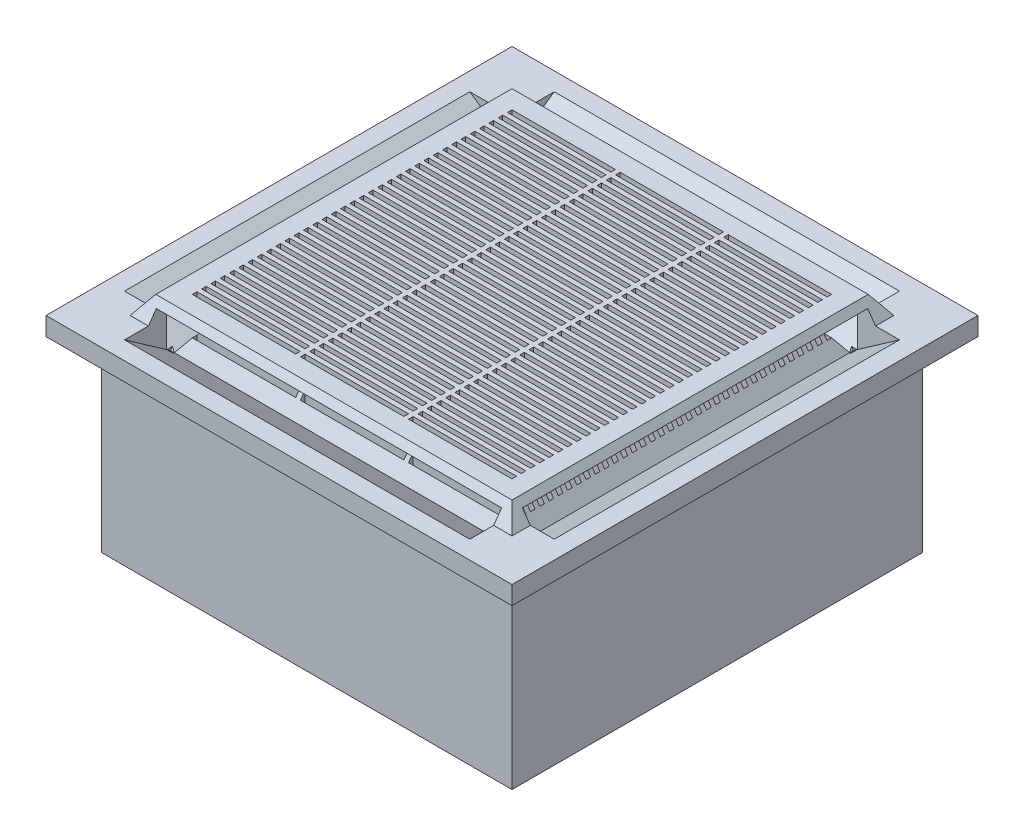
SolidWorks part; units mm, degrees
material "ABS"
ref_plane "Front Plane" through (0, 0, 0) normal (0, 0, 1) x (1, 0, 0)
ref_plane "Top Plane" through (0, 0, 0) normal (0, 1, 0) x (1, 0, 0)
ref_plane "Right Plane" through (0, 0, 0) normal (1, 0, 0) x (0, 0, -1)
sketch "Sketch1" plane through (0, 0, 0) normal (0, 1, 0) x (1, 0, 0)
  line L1 (-284.988, 284.988) -> (284.988, 284.988)
  line L2 (-284.988, 284.988) -> (-284.988, -284.988)
  line L3 (-284.988, -284.988) -> (284.988, -284.988)
  line L4 (284.988, 284.988) -> (284.988, -284.988)
  point P4 (0, 284.988)
  point P7 (-284.988, 0)
  dimension "D1" = 569.976
  dimension "D2" = 569.976
extrude "Boss-Extrude1" add sketch "Sketch1" along normal blind 260.096
sketch3d "3DSketch1"
  point P0 (-88.2401, 260.096, -68.0252)
ref_plane "Plane1" through (0, 260.096, 0) normal (0, 1, 0) x (1, 0, 0)
sketch "Sketch3" plane through (0, 260.096, 0) normal (0, 1, 0) x (1, 0, 0)
  line L1 (-322.961, 322.961) -> (323.977, 322.961)
  line L2 (-322.961, 322.961) -> (-322.961, -323.977)
  line L3 (-322.961, -323.977) -> (323.977, -323.977)
  line L4 (323.977, 322.961) -> (323.977, -323.977)
  dimension "D1" = 646.938
  dimension "D2" = 646.938
  dimension "D3" = 38.989
  dimension "D4" = 38.989
extrude "Boss-Extrude2" add sketch "Sketch3" along normal blind 50.8
sketch "Sketch4" plane through (0, 310.896, 0) normal (0, 1, 0) x (1, 0, 0)
  line L0 (-322.961, 322.961) -> (-322.961, -323.977) construction
  line L1 (-221.361, 221.361) -> (-77.851, 221.361)
  line L2 (-221.361, 221.361) -> (-221.361, 215.011)
  line L3 (-221.361, 215.011) -> (-77.851, 215.011)
  line L4 (-77.851, 221.361) -> (-77.851, 215.011)
  line L5 (323.977, 322.961) -> (-322.961, 322.961) construction
  line L6 (-71.247, 221.361) -> (72.263, 221.361)
  line L7 (-71.247, 221.361) -> (-71.247, 215.011)
  line L8 (-71.247, 215.011) -> (72.263, 215.011)
  line L9 (72.263, 221.361) -> (72.263, 215.011)
  line L10 (78.867, 221.361) -> (222.377, 221.361)
  line L11 (78.867, 221.361) -> (78.867, 215.011)
  line L12 (78.867, 215.011) -> (222.377, 215.011)
  line L13 (222.377, 221.361) -> (222.377, 215.011)
  line L14 (-71.247, 208.4966) -> (72.263, 208.4966)
  line L15 (-71.247, 208.4966) -> (-71.247, 202.1466)
  line L16 (-71.247, 202.1466) -> (72.263, 202.1466)
  line L17 (72.263, 208.4966) -> (72.263, 202.1466)
  line L18 (78.867, 208.4966) -> (222.377, 208.4966)
  line L19 (78.867, 208.4966) -> (78.867, 202.1466)
  line L20 (78.867, 202.1466) -> (222.377, 202.1466)
  line L21 (222.377, 208.4966) -> (222.377, 202.1466)
  line L22 (-71.247, 195.6323) -> (72.263, 195.6323)
  line L23 (-71.247, 195.6323) -> (-71.247, 189.2823)
  line L24 (-71.247, 189.2823) -> (72.263, 189.2823)
  line L25 (72.263, 195.6323) -> (72.263, 189.2823)
  line L26 (78.867, 195.6323) -> (222.377, 195.6323)
  line L27 (78.867, 195.6323) -> (78.867, 189.2823)
  line L28 (78.867, 189.2823) -> (222.377, 189.2823)
  line L29 (222.377, 195.6323) -> (222.377, 189.2823)
  line L30 (-71.247, 182.7679) -> (72.263, 182.7679)
  line L31 (-71.247, 182.7679) -> (-71.247, 176.4179)
  line L32 (-71.247, 176.4179) -> (72.263, 176.4179)
  line L33 (72.263, 182.7679) -> (72.263, 176.4179)
  line L34 (78.867, 182.7679) -> (222.377, 182.7679)
  line L35 (78.867, 182.7679) -> (78.867, 176.4179)
  line L36 (78.867, 176.4179) -> (222.377, 176.4179)
  line L37 (222.377, 182.7679) -> (222.377, 176.4179)
  line L38 (-71.247, 169.9036) -> (72.263, 169.9036)
  line L39 (-71.247, 169.9036) -> (-71.247, 163.5536)
  line L40 (-71.247, 163.5536) -> (72.263, 163.5536)
  line L41 (72.263, 169.9036) -> (72.263, 163.5536)
  line L42 (78.867, 169.9036) -> (222.377, 169.9036)
  line L43 (78.867, 169.9036) -> (78.867, 163.5536)
  line L44 (78.867, 163.5536) -> (222.377, 163.5536)
  line L45 (222.377, 169.9036) -> (222.377, 163.5536)
  line L46 (-71.247, 157.0392) -> (72.263, 157.0392)
  line L47 (-71.247, 157.0392) -> (-71.247, 150.6892)
  line L48 (-71.247, 150.6892) -> (72.263, 150.6892)
  line L49 (72.263, 157.0392) -> (72.263, 150.6892)
  line L50 (78.867, 157.0392) -> (222.377, 157.0392)
  line L51 (78.867, 157.0392) -> (78.867, 150.6892)
  line L52 (78.867, 150.6892) -> (222.377, 150.6892)
  line L53 (222.377, 157.0392) -> (222.377, 150.6892)
  line L54 (-71.247, 144.1749) -> (72.263, 144.1749)
  line L55 (-71.247, 144.1749) -> (-71.247, 137.8249)
  line L56 (-71.247, 137.8249) -> (72.263, 137.8249)
  line L57 (72.263, 144.1749) -> (72.263, 137.8249)
  line L58 (78.867, 144.1749) -> (222.377, 144.1749)
  line L59 (78.867, 144.1749) -> (78.867, 137.8249)
  line L60 (78.867, 137.8249) -> (222.377, 137.8249)
  line L61 (222.377, 144.1749) -> (222.377, 137.8249)
  line L62 (-71.247, 131.3105) -> (72.263, 131.3105)
  line L63 (-71.247, 131.3105) -> (-71.247, 124.9605)
  line L64 (-71.247, 124.9605) -> (72.263, 124.9605)
  line L65 (72.263, 131.3105) -> (72.263, 124.9605)
  line L66 (78.867, 131.3105) -> (222.377, 131.3105)
  line L67 (78.867, 131.3105) -> (78.867, 124.9605)
  line L68 (78.867, 124.9605) -> (222.377, 124.9605)
  line L69 (222.377, 131.3105) -> (222.377, 124.9605)
  line L70 (-71.247, 118.4462) -> (72.263, 118.4462)
  line L71 (-71.247, 118.4462) -> (-71.247, 112.0962)
  line L72 (-71.247, 112.0962) -> (72.263, 112.0962)
  line L73 (72.263, 118.4462) -> (72.263, 112.0962)
  line L74 (78.867, 118.4462) -> (222.377, 118.4462)
  line L75 (78.867, 118.4462) -> (78.867, 112.0962)
  line L76 (78.867, 112.0962) -> (222.377, 112.0962)
  line L77 (222.377, 118.4462) -> (222.377, 112.0962)
  line L78 (-71.247, 105.5818) -> (72.263, 105.5818)
  line L79 (-71.247, 105.5818) -> (-71.247, 99.2318)
  line L80 (-71.247, 99.2318) -> (72.263, 99.2318)
  line L81 (72.263, 105.5818) -> (72.263, 99.2318)
  line L82 (78.867, 105.5818) -> (222.377, 105.5818)
  line L83 (78.867, 105.5818) -> (78.867, 99.2318)
  line L84 (78.867, 99.2318) -> (222.377, 99.2318)
  line L85 (222.377, 105.5818) -> (222.377, 99.2318)
  line L86 (-71.247, 92.7175) -> (72.263, 92.7175)
  line L87 (-71.247, 92.7175) -> (-71.247, 86.3675)
  line L88 (-71.247, 86.3675) -> (72.263, 86.3675)
  line L89 (72.263, 92.7175) -> (72.263, 86.3675)
  line L90 (78.867, 92.7175) -> (222.377, 92.7175)
  line L91 (78.867, 92.7175) -> (78.867, 86.3675)
  line L92 (78.867, 86.3675) -> (222.377, 86.3675)
  line L93 (222.377, 92.7175) -> (222.377, 86.3675)
  line L94 (-71.247, 79.8531) -> (72.263, 79.8531)
  line L95 (-71.247, 79.8531) -> (-71.247, 73.5031)
  line L96 (-71.247, 73.5031) -> (72.263, 73.5031)
  line L97 (72.263, 79.8531) -> (72.263, 73.5031)
  line L98 (78.867, 79.8531) -> (222.377, 79.8531)
  line L99 (78.867, 79.8531) -> (78.867, 73.5031)
  line L100 (78.867, 73.5031) -> (222.377, 73.5031)
  line L101 (222.377, 79.8531) -> (222.377, 73.5031)
  line L102 (-71.247, 66.9888) -> (72.263, 66.9888)
  line L103 (-71.247, 66.9888) -> (-71.247, 60.6388)
  line L104 (-71.247, 60.6388) -> (72.263, 60.6388)
  line L105 (72.263, 66.9888) -> (72.263, 60.6388)
  line L106 (78.867, 66.9888) -> (222.377, 66.9888)
  line L107 (78.867, 66.9888) -> (78.867, 60.6388)
  line L108 (78.867, 60.6388) -> (222.377, 60.6388)
  line L109 (222.377, 66.9888) -> (222.377, 60.6388)
  line L110 (-71.247, 54.1244) -> (72.263, 54.1244)
  line L111 (-71.247, 54.1244) -> (-71.247, 47.7744)
  line L112 (-71.247, 47.7744) -> (72.263, 47.7744)
  line L113 (72.263, 54.1244) -> (72.263, 47.7744)
  line L114 (78.867, 54.1244) -> (222.377, 54.1244)
  line L115 (78.867, 54.1244) -> (78.867, 47.7744)
  line L116 (78.867, 47.7744) -> (222.377, 47.7744)
  line L117 (222.377, 54.1244) -> (222.377, 47.7744)
  line L118 (-71.247, 41.2601) -> (72.263, 41.2601)
  line L119 (-71.247, 41.2601) -> (-71.247, 34.9101)
  line L120 (-71.247, 34.9101) -> (72.263, 34.9101)
  line L121 (72.263, 41.2601) -> (72.263, 34.9101)
  line L122 (78.867, 41.2601) -> (222.377, 41.2601)
  line L123 (78.867, 41.2601) -> (78.867, 34.9101)
  line L124 (78.867, 34.9101) -> (222.377, 34.9101)
  line L125 (222.377, 41.2601) -> (222.377, 34.9101)
  line L126 (-71.247, 28.3957) -> (72.263, 28.3957)
  line L127 (-71.247, 28.3957) -> (-71.247, 22.0457)
  line L128 (-71.247, 22.0457) -> (72.263, 22.0457)
  line L129 (72.263, 28.3957) -> (72.263, 22.0457)
  line L130 (78.867, 28.3957) -> (222.377, 28.3957)
  line L131 (78.867, 28.3957) -> (78.867, 22.0457)
  line L132 (78.867, 22.0457) -> (222.377, 22.0457)
  line L133 (222.377, 28.3957) -> (222.377, 22.0457)
  line L134 (-71.247, 15.5314) -> (72.263, 15.5314)
  line L135 (-71.247, 15.5314) -> (-71.247, 9.1814)
  line L136 (-71.247, 9.1814) -> (72.263, 9.1814)
  line L137 (72.263, 15.5314) -> (72.263, 9.1814)
  line L138 (78.867, 15.5314) -> (222.377, 15.5314)
  line L139 (78.867, 15.5314) -> (78.867, 9.1814)
  line L140 (78.867, 9.1814) -> (222.377, 9.1814)
  line L141 (222.377, 15.5314) -> (222.377, 9.1814)
  line L142 (-71.247, 2.667) -> (72.263, 2.667)
  line L143 (-71.247, 2.667) -> (-71.247, -3.683)
  line L144 (-71.247, -3.683) -> (72.263, -3.683)
  line L145 (72.263, 2.667) -> (72.263, -3.683)
  line L146 (78.867, 2.667) -> (222.377, 2.667)
  line L147 (78.867, 2.667) -> (78.867, -3.683)
  line L148 (78.867, -3.683) -> (222.377, -3.683)
  line L149 (222.377, 2.667) -> (222.377, -3.683)
  line L150 (-71.247, -10.1974) -> (72.263, -10.1974)
  line L151 (-71.247, -10.1974) -> (-71.247, -16.5474)
  line L152 (-71.247, -16.5474) -> (72.263, -16.5474)
  line L153 (72.263, -10.1974) -> (72.263, -16.5474)
  line L154 (78.867, -10.1974) -> (222.377, -10.1974)
  line L155 (78.867, -10.1974) -> (78.867, -16.5474)
  line L156 (78.867, -16.5474) -> (222.377, -16.5474)
  line L157 (222.377, -10.1974) -> (222.377, -16.5474)
  line L158 (-71.247, -23.0617) -> (72.263, -23.0617)
  line L159 (-71.247, -23.0617) -> (-71.247, -29.4117)
  line L160 (-71.247, -29.4117) -> (72.263, -29.4117)
  line L161 (72.263, -23.0617) -> (72.263, -29.4117)
  line L162 (78.867, -23.0617) -> (222.377, -23.0617)
  line L163 (78.867, -23.0617) -> (78.867, -29.4117)
  line L164 (78.867, -29.4117) -> (222.377, -29.4117)
  line L165 (222.377, -23.0617) -> (222.377, -29.4117)
  line L166 (-71.247, -35.9261) -> (72.263, -35.9261)
  line L167 (-71.247, -35.9261) -> (-71.247, -42.2761)
  line L168 (-71.247, -42.2761) -> (72.263, -42.2761)
  line L169 (72.263, -35.9261) -> (72.263, -42.2761)
  line L170 (78.867, -35.9261) -> (222.377, -35.9261)
  line L171 (78.867, -35.9261) -> (78.867, -42.2761)
  line L172 (78.867, -42.2761) -> (222.377, -42.2761)
  line L173 (222.377, -35.9261) -> (222.377, -42.2761)
  line L174 (-71.247, -48.7904) -> (72.263, -48.7904)
  line L175 (-71.247, -48.7904) -> (-71.247, -55.1404)
  line L176 (-71.247, -55.1404) -> (72.263, -55.1404)
  line L177 (72.263, -48.7904) -> (72.263, -55.1404)
  line L178 (78.867, -48.7904) -> (222.377, -48.7904)
  line L179 (78.867, -48.7904) -> (78.867, -55.1404)
  line L180 (78.867, -55.1404) -> (222.377, -55.1404)
  line L181 (222.377, -48.7904) -> (222.377, -55.1404)
  line L182 (-71.247, -61.6548) -> (72.263, -61.6548)
  line L183 (-71.247, -61.6548) -> (-71.247, -68.0048)
  line L184 (-71.247, -68.0048) -> (72.263, -68.0048)
  line L185 (72.263, -61.6548) -> (72.263, -68.0048)
  line L186 (78.867, -61.6548) -> (222.377, -61.6548)
  line L187 (78.867, -61.6548) -> (78.867, -68.0048)
  line L188 (78.867, -68.0048) -> (222.377, -68.0048)
  line L189 (222.377, -61.6548) -> (222.377, -68.0048)
  line L190 (-71.247, -74.5191) -> (72.263, -74.5191)
  line L191 (-71.247, -74.5191) -> (-71.247, -80.8691)
  line L192 (-71.247, -80.8691) -> (72.263, -80.8691)
  line L193 (72.263, -74.5191) -> (72.263, -80.8691)
  line L194 (78.867, -74.5191) -> (222.377, -74.5191)
  line L195 (78.867, -74.5191) -> (78.867, -80.8691)
  line L196 (78.867, -80.8691) -> (222.377, -80.8691)
  line L197 (222.377, -74.5191) -> (222.377, -80.8691)
  line L198 (-71.247, -87.3835) -> (72.263, -87.3835)
  line L199 (-71.247, -87.3835) -> (-71.247, -93.7335)
  line L200 (-71.247, -93.7335) -> (72.263, -93.7335)
  line L201 (72.263, -87.3835) -> (72.263, -93.7335)
  line L202 (78.867, -87.3835) -> (222.377, -87.3835)
  line L203 (78.867, -87.3835) -> (78.867, -93.7335)
  line L204 (78.867, -93.7335) -> (222.377, -93.7335)
  line L205 (222.377, -87.3835) -> (222.377, -93.7335)
  line L206 (-71.247, -100.2478) -> (72.263, -100.2478)
  line L207 (-71.247, -100.2478) -> (-71.247, -106.5978)
  line L208 (-71.247, -106.5978) -> (72.263, -106.5978)
  line L209 (72.263, -100.2478) -> (72.263, -106.5978)
  line L210 (78.867, -100.2478) -> (222.377, -100.2478)
  line L211 (78.867, -100.2478) -> (78.867, -106.5978)
  line L212 (78.867, -106.5978) -> (222.377, -106.5978)
  line L213 (222.377, -100.2478) -> (222.377, -106.5978)
  line L214 (-71.247, -113.1122) -> (72.263, -113.1122)
  line L215 (-71.247, -113.1122) -> (-71.247, -119.4622)
  line L216 (-71.247, -119.4622) -> (72.263, -119.4622)
  line L217 (72.263, -113.1122) -> (72.263, -119.4622)
  line L218 (78.867, -113.1122) -> (222.377, -113.1122)
  line L219 (78.867, -113.1122) -> (78.867, -119.4622)
  line L220 (78.867, -119.4622) -> (222.377, -119.4622)
  line L221 (222.377, -113.1122) -> (222.377, -119.4622)
  line L222 (-71.247, -125.9765) -> (72.263, -125.9765)
  line L223 (-71.247, -125.9765) -> (-71.247, -132.3265)
  line L224 (-71.247, -132.3265) -> (72.263, -132.3265)
  line L225 (72.263, -125.9765) -> (72.263, -132.3265)
  line L226 (78.867, -125.9765) -> (222.377, -125.9765)
  line L227 (78.867, -125.9765) -> (78.867, -132.3265)
  line L228 (78.867, -132.3265) -> (222.377, -132.3265)
  line L229 (222.377, -125.9765) -> (222.377, -132.3265)
  line L230 (-71.247, -138.8409) -> (72.263, -138.8409)
  line L231 (-71.247, -138.8409) -> (-71.247, -145.1909)
  line L232 (-71.247, -145.1909) -> (72.263, -145.1909)
  line L233 (72.263, -138.8409) -> (72.263, -145.1909)
  line L234 (78.867, -138.8409) -> (222.377, -138.8409)
  line L235 (78.867, -138.8409) -> (78.867, -145.1909)
  line L236 (78.867, -145.1909) -> (222.377, -145.1909)
  line L237 (222.377, -138.8409) -> (222.377, -145.1909)
  line L238 (-71.247, -151.7052) -> (72.263, -151.7052)
  line L239 (-71.247, -151.7052) -> (-71.247, -158.0552)
  line L240 (-71.247, -158.0552) -> (72.263, -158.0552)
  line L241 (72.263, -151.7052) -> (72.263, -158.0552)
  line L242 (78.867, -151.7052) -> (222.377, -151.7052)
  line L243 (78.867, -151.7052) -> (78.867, -158.0552)
  line L244 (78.867, -158.0552) -> (222.377, -158.0552)
  line L245 (222.377, -151.7052) -> (222.377, -158.0552)
  line L246 (-71.247, -164.5696) -> (72.263, -164.5696)
  line L247 (-71.247, -164.5696) -> (-71.247, -170.9196)
  line L248 (-71.247, -170.9196) -> (72.263, -170.9196)
  line L249 (72.263, -164.5696) -> (72.263, -170.9196)
  line L250 (78.867, -164.5696) -> (222.377, -164.5696)
  line L251 (78.867, -164.5696) -> (78.867, -170.9196)
  line L252 (78.867, -170.9196) -> (222.377, -170.9196)
  line L253 (222.377, -164.5696) -> (222.377, -170.9196)
  line L254 (-71.247, -177.4339) -> (72.263, -177.4339)
  line L255 (-71.247, -177.4339) -> (-71.247, -183.7839)
  line L256 (-71.247, -183.7839) -> (72.263, -183.7839)
  line L257 (72.263, -177.4339) -> (72.263, -183.7839)
  line L258 (78.867, -177.4339) -> (222.377, -177.4339)
  line L259 (78.867, -177.4339) -> (78.867, -183.7839)
  line L260 (78.867, -183.7839) -> (222.377, -183.7839)
  line L261 (222.377, -177.4339) -> (222.377, -183.7839)
  line L262 (-71.247, -190.2983) -> (72.263, -190.2983)
  line L263 (-71.247, -190.2983) -> (-71.247, -196.6483)
  line L264 (-71.247, -196.6483) -> (72.263, -196.6483)
  line L265 (72.263, -190.2983) -> (72.263, -196.6483)
  line L266 (78.867, -190.2983) -> (222.377, -190.2983)
  line L267 (78.867, -190.2983) -> (78.867, -196.6483)
  line L268 (78.867, -196.6483) -> (222.377, -196.6483)
  line L269 (222.377, -190.2983) -> (222.377, -196.6483)
  line L270 (-71.247, -203.1626) -> (72.263, -203.1626)
  line L271 (-71.247, -203.1626) -> (-71.247, -209.5126)
  line L272 (-71.247, -209.5126) -> (72.263, -209.5126)
  line L273 (72.263, -203.1626) -> (72.263, -209.5126)
  line L274 (78.867, -203.1626) -> (222.377, -203.1626)
  line L275 (78.867, -203.1626) -> (78.867, -209.5126)
  line L276 (78.867, -209.5126) -> (222.377, -209.5126)
  line L277 (222.377, -203.1626) -> (222.377, -209.5126)
  line L278 (-71.247, -216.027) -> (72.263, -216.027)
  line L279 (-71.247, -216.027) -> (-71.247, -222.377)
  line L280 (-71.247, -222.377) -> (72.263, -222.377)
  line L281 (72.263, -216.027) -> (72.263, -222.377)
  line L282 (78.867, -216.027) -> (222.377, -216.027)
  line L283 (78.867, -216.027) -> (78.867, -222.377)
  line L284 (78.867, -222.377) -> (222.377, -222.377)
  line L285 (222.377, -216.027) -> (222.377, -222.377)
  line L286 (-221.361, 208.4966) -> (-77.851, 208.4966)
  line L287 (-221.361, 208.4966) -> (-221.361, 202.1466)
  line L288 (-221.361, 202.1466) -> (-77.851, 202.1466)
  line L289 (-77.851, 208.4966) -> (-77.851, 202.1466)
  line L290 (-221.361, 195.6323) -> (-77.851, 195.6323)
  line L291 (-221.361, 195.6323) -> (-221.361, 189.2823)
  line L292 (-221.361, 189.2823) -> (-77.851, 189.2823)
  line L293 (-77.851, 195.6323) -> (-77.851, 189.2823)
  line L294 (-221.361, 182.7679) -> (-77.851, 182.7679)
  line L295 (-221.361, 182.7679) -> (-221.361, 176.4179)
  line L296 (-221.361, 176.4179) -> (-77.851, 176.4179)
  line L297 (-77.851, 182.7679) -> (-77.851, 176.4179)
  line L298 (-221.361, 169.9036) -> (-77.851, 169.9036)
  line L299 (-221.361, 169.9036) -> (-221.361, 163.5536)
  line L300 (-221.361, 163.5536) -> (-77.851, 163.5536)
  line L301 (-77.851, 169.9036) -> (-77.851, 163.5536)
  line L302 (-221.361, 157.0392) -> (-77.851, 157.0392)
  line L303 (-221.361, 157.0392) -> (-221.361, 150.6892)
  line L304 (-221.361, 150.6892) -> (-77.851, 150.6892)
  line L305 (-77.851, 157.0392) -> (-77.851, 150.6892)
  line L306 (-221.361, 144.1749) -> (-77.851, 144.1749)
  line L307 (-221.361, 144.1749) -> (-221.361, 137.8249)
  line L308 (-221.361, 137.8249) -> (-77.851, 137.8249)
  line L309 (-77.851, 144.1749) -> (-77.851, 137.8249)
  line L310 (-221.361, 131.3105) -> (-77.851, 131.3105)
  line L311 (-221.361, 131.3105) -> (-221.361, 124.9605)
  line L312 (-221.361, 124.9605) -> (-77.851, 124.9605)
  line L313 (-77.851, 131.3105) -> (-77.851, 124.9605)
  line L314 (-221.361, 118.4462) -> (-77.851, 118.4462)
  line L315 (-221.361, 118.4462) -> (-221.361, 112.0962)
  line L316 (-221.361, 112.0962) -> (-77.851, 112.0962)
  line L317 (-77.851, 118.4462) -> (-77.851, 112.0962)
  line L318 (-221.361, 105.5818) -> (-77.851, 105.5818)
  line L319 (-221.361, 105.5818) -> (-221.361, 99.2318)
  line L320 (-221.361, 99.2318) -> (-77.851, 99.2318)
  line L321 (-77.851, 105.5818) -> (-77.851, 99.2318)
  line L322 (-221.361, 92.7175) -> (-77.851, 92.7175)
  line L323 (-221.361, 92.7175) -> (-221.361, 86.3675)
  line L324 (-221.361, 86.3675) -> (-77.851, 86.3675)
  line L325 (-77.851, 92.7175) -> (-77.851, 86.3675)
  line L326 (-221.361, 79.8531) -> (-77.851, 79.8531)
  line L327 (-221.361, 79.8531) -> (-221.361, 73.5031)
  line L328 (-221.361, 73.5031) -> (-77.851, 73.5031)
  line L329 (-77.851, 79.8531) -> (-77.851, 73.5031)
  line L330 (-221.361, 66.9888) -> (-77.851, 66.9888)
  line L331 (-221.361, 66.9888) -> (-221.361, 60.6388)
  line L332 (-221.361, 60.6388) -> (-77.851, 60.6388)
  line L333 (-77.851, 66.9888) -> (-77.851, 60.6388)
  line L334 (-221.361, 54.1244) -> (-77.851, 54.1244)
  line L335 (-221.361, 54.1244) -> (-221.361, 47.7744)
  line L336 (-221.361, 47.7744) -> (-77.851, 47.7744)
  line L337 (-77.851, 54.1244) -> (-77.851, 47.7744)
  line L338 (-221.361, 41.2601) -> (-77.851, 41.2601)
  line L339 (-221.361, 41.2601) -> (-221.361, 34.9101)
  line L340 (-221.361, 34.9101) -> (-77.851, 34.9101)
  line L341 (-77.851, 41.2601) -> (-77.851, 34.9101)
  line L342 (-221.361, 28.3957) -> (-77.851, 28.3957)
  line L343 (-221.361, 28.3957) -> (-221.361, 22.0457)
  line L344 (-221.361, 22.0457) -> (-77.851, 22.0457)
  line L345 (-77.851, 28.3957) -> (-77.851, 22.0457)
  line L346 (-221.361, 15.5314) -> (-77.851, 15.5314)
  line L347 (-221.361, 15.5314) -> (-221.361, 9.1814)
  line L348 (-221.361, 9.1814) -> (-77.851, 9.1814)
  line L349 (-77.851, 15.5314) -> (-77.851, 9.1814)
  line L350 (-221.361, 2.667) -> (-77.851, 2.667)
  line L351 (-221.361, 2.667) -> (-221.361, -3.683)
  line L352 (-221.361, -3.683) -> (-77.851, -3.683)
  line L353 (-77.851, 2.667) -> (-77.851, -3.683)
  line L354 (-221.361, -10.1974) -> (-77.851, -10.1974)
  line L355 (-221.361, -10.1974) -> (-221.361, -16.5474)
  line L356 (-221.361, -16.5474) -> (-77.851, -16.5474)
  line L357 (-77.851, -10.1974) -> (-77.851, -16.5474)
  line L358 (-221.361, -23.0617) -> (-77.851, -23.0617)
  line L359 (-221.361, -23.0617) -> (-221.361, -29.4117)
  line L360 (-221.361, -29.4117) -> (-77.851, -29.4117)
  line L361 (-77.851, -23.0617) -> (-77.851, -29.4117)
  line L362 (-221.361, -35.9261) -> (-77.851, -35.9261)
  line L363 (-221.361, -35.9261) -> (-221.361, -42.2761)
  line L364 (-221.361, -42.2761) -> (-77.851, -42.2761)
  line L365 (-77.851, -35.9261) -> (-77.851, -42.2761)
  line L366 (-221.361, -48.7904) -> (-77.851, -48.7904)
  line L367 (-221.361, -48.7904) -> (-221.361, -55.1404)
  line L368 (-221.361, -55.1404) -> (-77.851, -55.1404)
  line L369 (-77.851, -48.7904) -> (-77.851, -55.1404)
  line L370 (-221.361, -61.6548) -> (-77.851, -61.6548)
  line L371 (-221.361, -61.6548) -> (-221.361, -68.0048)
  line L372 (-221.361, -68.0048) -> (-77.851, -68.0048)
  line L373 (-77.851, -61.6548) -> (-77.851, -68.0048)
  line L374 (-221.361, -74.5191) -> (-77.851, -74.5191)
  line L375 (-221.361, -74.5191) -> (-221.361, -80.8691)
  line L376 (-221.361, -80.8691) -> (-77.851, -80.8691)
  line L377 (-77.851, -74.5191) -> (-77.851, -80.8691)
  line L378 (-221.361, -87.3835) -> (-77.851, -87.3835)
  line L379 (-221.361, -87.3835) -> (-221.361, -93.7335)
  line L380 (-221.361, -93.7335) -> (-77.851, -93.7335)
  line L381 (-77.851, -87.3835) -> (-77.851, -93.7335)
  line L382 (-221.361, -100.2478) -> (-77.851, -100.2478)
  line L383 (-221.361, -100.2478) -> (-221.361, -106.5978)
  line L384 (-221.361, -106.5978) -> (-77.851, -106.5978)
  line L385 (-77.851, -100.2478) -> (-77.851, -106.5978)
  line L386 (-221.361, -113.1122) -> (-77.851, -113.1122)
  line L387 (-221.361, -113.1122) -> (-221.361, -119.4622)
  line L388 (-221.361, -119.4622) -> (-77.851, -119.4622)
  line L389 (-77.851, -113.1122) -> (-77.851, -119.4622)
  line L390 (-221.361, -125.9765) -> (-77.851, -125.9765)
  line L391 (-221.361, -125.9765) -> (-221.361, -132.3265)
  line L392 (-221.361, -132.3265) -> (-77.851, -132.3265)
  line L393 (-77.851, -125.9765) -> (-77.851, -132.3265)
  line L394 (-221.361, -138.8409) -> (-77.851, -138.8409)
  line L395 (-221.361, -138.8409) -> (-221.361, -145.1909)
  line L396 (-221.361, -145.1909) -> (-77.851, -145.1909)
  line L397 (-77.851, -138.8409) -> (-77.851, -145.1909)
  line L398 (-221.361, -151.7052) -> (-77.851, -151.7052)
  line L399 (-221.361, -151.7052) -> (-221.361, -158.0552)
  line L400 (-221.361, -158.0552) -> (-77.851, -158.0552)
  line L401 (-77.851, -151.7052) -> (-77.851, -158.0552)
  line L402 (-221.361, -164.5696) -> (-77.851, -164.5696)
  line L403 (-221.361, -164.5696) -> (-221.361, -170.9196)
  line L404 (-221.361, -170.9196) -> (-77.851, -170.9196)
  line L405 (-77.851, -164.5696) -> (-77.851, -170.9196)
  line L406 (-221.361, -177.4339) -> (-77.851, -177.4339)
  line L407 (-221.361, -177.4339) -> (-221.361, -183.7839)
  line L408 (-221.361, -183.7839) -> (-77.851, -183.7839)
  line L409 (-77.851, -177.4339) -> (-77.851, -183.7839)
  line L410 (-221.361, -190.2983) -> (-77.851, -190.2983)
  line L411 (-221.361, -190.2983) -> (-221.361, -196.6483)
  line L412 (-221.361, -196.6483) -> (-77.851, -196.6483)
  line L413 (-77.851, -190.2983) -> (-77.851, -196.6483)
  line L414 (-221.361, -203.1626) -> (-77.851, -203.1626)
  line L415 (-221.361, -203.1626) -> (-221.361, -209.5126)
  line L416 (-221.361, -209.5126) -> (-77.851, -209.5126)
  line L417 (-77.851, -203.1626) -> (-77.851, -209.5126)
  line L418 (-221.361, -216.027) -> (-77.851, -216.027)
  line L419 (-221.361, -216.027) -> (-221.361, -222.377)
  line L420 (-221.361, -222.377) -> (-77.851, -222.377)
  line L421 (-77.851, -216.027) -> (-77.851, -222.377)
  line L423 (-322.961, -323.977) -> (323.977, -323.977) construction
  line L424 (323.977, -323.977) -> (323.977, 322.961) construction
  point P8 (349.8775, -293.0368)
  point P429 (0, 0)
  point P430 (0, 0)
  point P431 (0, 0)
  point P432 (0, 0)
  point P433 (0, 0)
  dimension "D1" = 101.6
  dimension "D2" = 101.6
  dimension "D3" = 6.35
  dimension "D4" = 143.51
  dimension "D7" = 101.6
  dimension "D8" = 101.6
  dimension "D9" = 101.6
  dimension "D5" = 3
  dimension "D6" = 35
extrude "Cut-Extrude2" cut sketch "Sketch4" against normal blind 101.6
sketch "Sketch5" plane through (0, 310.896, 0) normal (0, 1, 0) x (1, 0, 0)
  line L0 (323.977, 322.961) -> (-322.961, 322.961) construction
  line L1 (-399.161, -400.177) -> (400.177, -400.177)
  line L2 (-399.161, -400.177) -> (-399.161, 399.161)
  line L3 (-399.161, 399.161) -> (400.177, 399.161)
  line L4 (400.177, -400.177) -> (400.177, 399.161)
  line L5 (247.777, 246.761) -> (-246.761, 246.761)
  line L6 (247.777, 246.761) -> (247.777, -247.777)
  line L7 (247.777, -247.777) -> (-246.761, -247.777)
  line L8 (-246.761, 246.761) -> (-246.761, -247.777)
  line L9 (-322.961, 322.961) -> (-322.961, -323.977) construction
  line L10 (-322.961, -323.977) -> (323.977, -323.977) construction
  line L11 (323.977, -323.977) -> (323.977, 322.961) construction
  point P10 (0, 0)
  point P11 (0, 0)
  point P12 (-279.347, -430.6918)
  point P17 (-299.2396, 366.2951)
  dimension "D1" = 76.2
  dimension "D2" = 76.2
  dimension "D3" = 76.2
  dimension "D4" = 76.2
  dimension "D5" = 76.2
  dimension "D6" = 76.2
  dimension "D7" = 76.2
extrude "Cut-Extrude3" cut sketch "Sketch5" against normal blind 25.4 draft 35
sketch "Sketch6" plane through (312.3342, 218.6988, 0) normal (0.8192, 0.5736, 0) x (0, 0, -1)
  line L0 (-265.5623, 81.5444) -> (264.5463, 81.5444) construction
  line L1 (-240.1623, 62.4944) -> (239.1463, 62.4944)
  line L2 (-240.1623, 62.4944) -> (-240.1623, 100.5944)
  line L3 (-240.1623, 100.5944) -> (239.1463, 100.5944)
  line L4 (239.1463, 62.4944) -> (239.1463, 100.5944)
  point P4 (239.1463, 81.5444)
  point P10 (-240.1623, 81.5444)
  dimension "D1" = 25.4
  dimension "D2" = 25.4
  dimension "D3" = 38.1
extrude "Cut-Extrude4" cut sketch "Sketch6" against normal mid plane 101.6
sketch "Sketch7" plane through (0, 218.2214, -311.6525) normal (0, 0.5736, -0.8192) x (-1, 0, 0)
  line L0 (-265.5623, 82.1271) -> (264.5463, 82.1271) construction
  line L1 (-240.1623, 101.1771) -> (239.1463, 101.1771)
  line L2 (-240.1623, 101.1771) -> (-240.1623, 63.0771)
  line L3 (-240.1623, 63.0771) -> (239.1463, 63.0771)
  line L4 (239.1463, 101.1771) -> (239.1463, 63.0771)
  point P4 (239.1463, 82.1271)
  point P6 (-240.1623, 82.1271)
  dimension "D1" = 25.4
  dimension "D2" = 25.4
  dimension "D3" = 38.1
extrude "Cut-Extrude5" cut sketch "Sketch7" against normal mid plane 101.6
sketch "Sketch8" plane through (-311.6525, 218.2214, 0) normal (-0.8192, 0.5736, 0) x (0, 0, 1)
  line L0 (-264.5463, 82.1271) -> (265.5623, 82.1271) construction
  line L1 (-239.1463, 101.1771) -> (240.1623, 101.1771)
  line L2 (-239.1463, 101.1771) -> (-239.1463, 63.0771)
  line L3 (-239.1463, 63.0771) -> (240.1623, 63.0771)
  line L4 (240.1623, 101.1771) -> (240.1623, 63.0771)
  point P4 (240.1623, 82.1271)
  dimension "D1" = 25.4
  dimension "D2" = 25.4
  dimension "D3" = 38.1
extrude "Cut-Extrude6" cut sketch "Sketch8" against normal mid plane 101.6
sketch "Sketch9" plane through (0, 218.6988, 312.3342) normal (0, 0.5736, 0.8192) x (1, 0, 0)
  line L0 (-264.5463, 81.5444) -> (265.5623, 81.5444) construction
  line L1 (-239.1463, 100.5944) -> (240.1623, 100.5944)
  line L2 (-239.1463, 100.5944) -> (-239.1463, 62.4944)
  line L3 (-239.1463, 62.4944) -> (240.1623, 62.4944)
  line L4 (240.1623, 100.5944) -> (240.1623, 62.4944)
  point P4 (-239.1463, 81.5444)
  dimension "D1" = 25.4
  dimension "D2" = 25.4
  dimension "D3" = 38.1
extrude "Cut-Extrude7" cut sketch "Sketch9" against normal mid plane 101.6
ref_plane "Plane2" through (0, 12.7, 0) normal (0, -1, 0) x (-1, 0, 0)
sketch "Sketch10" plane through (0, 12.7, 0) normal (0, -1, 0) x (-1, 0, 0)
  line L0 (284.988, -284.988) -> (-284.988, -284.988) construction
  line L1 (272.288, -272.288) -> (-272.288, -272.288)
  line L2 (272.288, -272.288) -> (272.288, 272.288)
  line L3 (272.288, 272.288) -> (-272.288, 272.288)
  line L4 (-272.288, -272.288) -> (-272.288, 272.288)
  line L5 (-284.988, 284.988) -> (284.988, 284.988) construction
  line L6 (-284.988, -284.988) -> (-284.988, 284.988) construction
  line L7 (284.988, 284.988) -> (284.988, -284.988) construction
  dimension "D1" = 12.7
  dimension "D2" = 12.7
  dimension "D3" = 12.7
  dimension "D4" = 12.7
extrude "Cut-Extrude8" cut sketch "Sketch10" against normal offset from surface (221.996 mm away) 25.4 up to face at (0.508, 260.096, 0.508)
